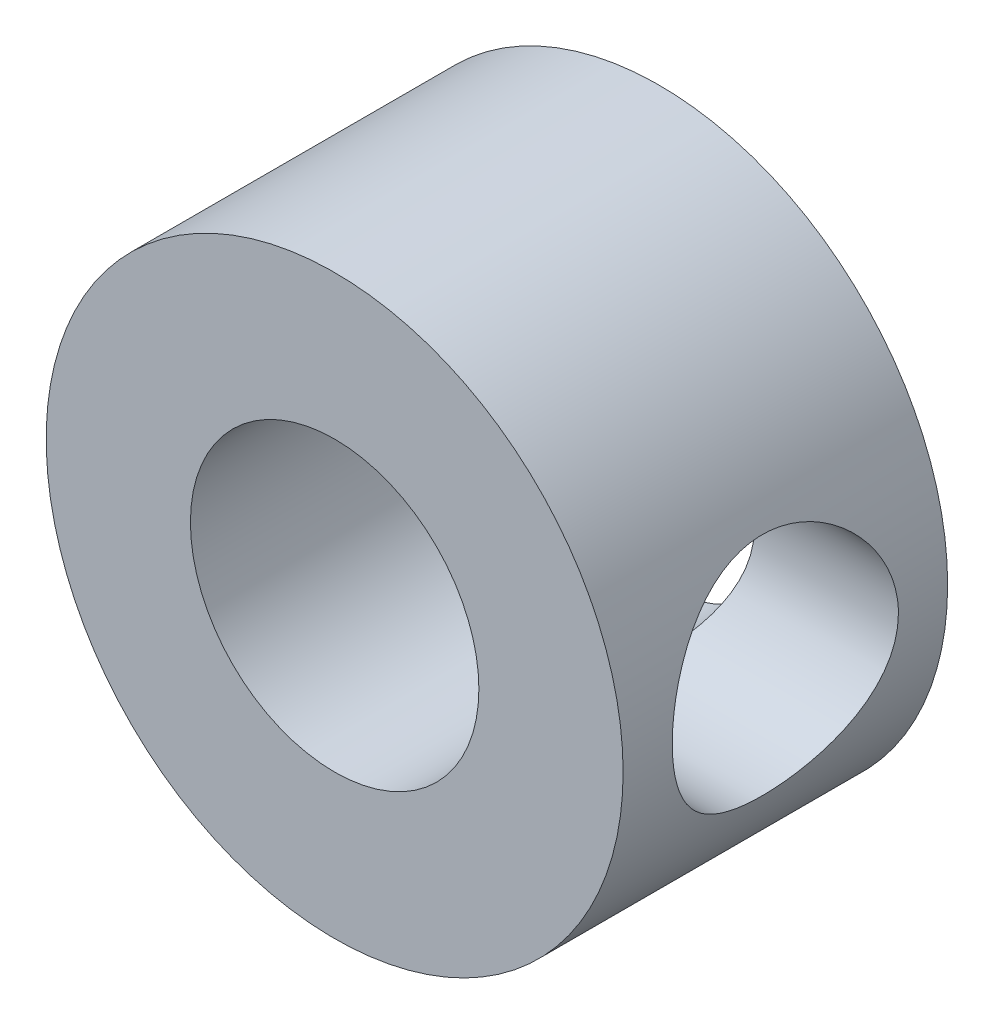
SolidWorks part; units mm, degrees
ref_plane "Front Plane" through (0, 0, 0) normal (0, 0, 1) x (1, 0, 0)
ref_plane "Top Plane" through (0, 0, 0) normal (0, 1, 0) x (1, 0, 0)
ref_plane "Right Plane" through (0, 0, 0) normal (1, 0, 0) x (0, 0, -1)
sketch "Sketch1" plane through (0, 0, 0) normal (0, 0, 1) x (1, 0, 0)
  circle A0 centre (0, 0) radius 3.175
  circle A1 centre (0, 0) radius 6.35
extrude "Extrude1" add sketch "Sketch1" along normal blind 7.1437
sketch "Sketch3" plane through (0, 0, 0) normal (0, 0, 1) x (1, 0, 0)
  line L0 (0, 0) -> (6.35, 0) construction
  circle A0 centre (0, 0) radius 6.35 construction
ref_plane "Plane1" through (6.35, 0, 0) normal (1, 0, 0) x (0, 0, -1)
sketch "Sketch4" plane through (6.35, 0, 0) normal (1, 0, 0) x (0, 0, -1)
  line L0 (0, 0) -> (-7.1451, 0) construction
  line L1 (-7.1451, 0) -> (-3.5726, 0) construction
hole_wizard "#9 (0.196) Diameter Hole2" positions "Sketch7" profile "Sketch6" hole size "#9" standard "Ansi Inch"
sketch "Sketch7" plane through (6.35, 0, 0) normal (1, 0, 0) x (0, 0, -1)
  point P1 (-3.5726, 0)
sketch "Sketch6" plane through (6.35, 0, 3.5726) normal (0, 1, 0) x (0, 0, -1)
  line L0 (0, 0) -> (0, 3.175)
  line L1 (0, 3.175) -> (2.4892, 3.175)
  line L2 (2.4892, 3.175) -> (2.4892, 0)
  line L5 (2.4892, 0) -> (0, 0)
  line L11 (0, -6.35) -> (0, 107.95) construction
  dimension "Thru Hole Dia." = 4.9784
  dimension "Thru Hole Depth" = 3.175
